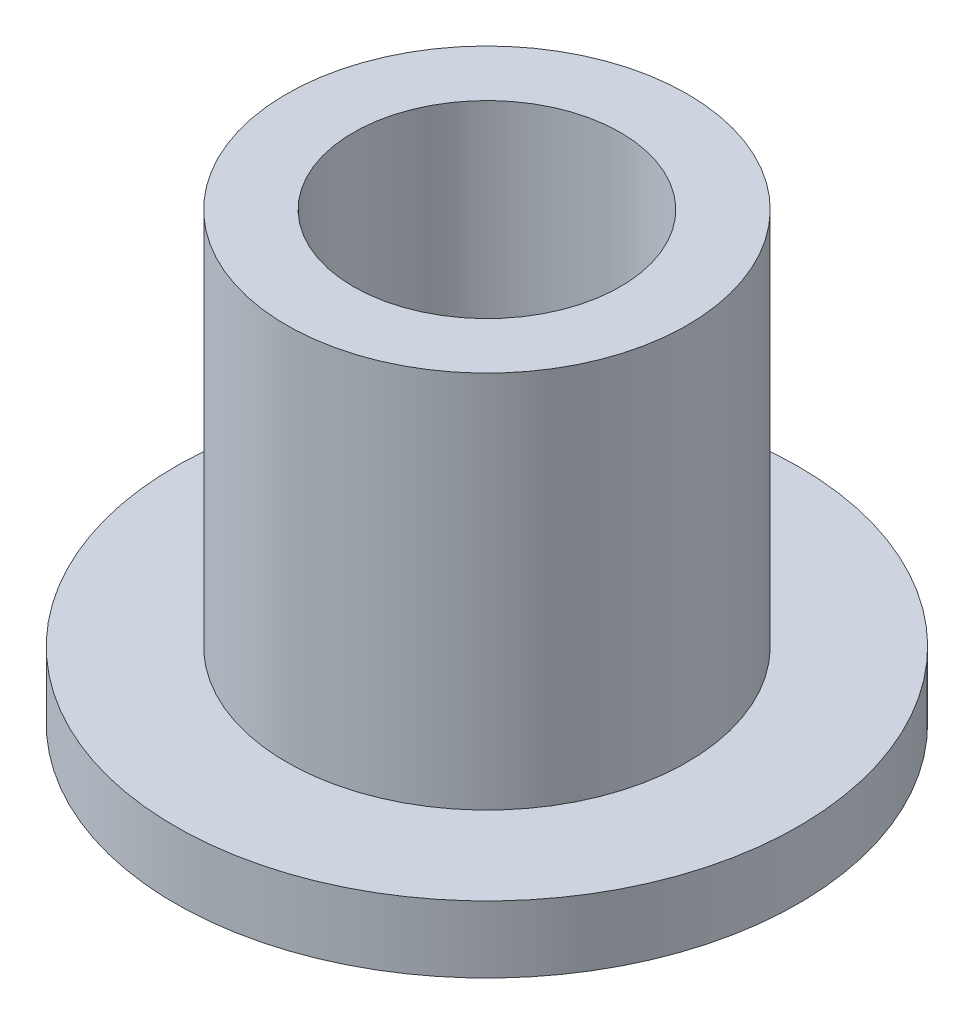
SolidWorks part; units mm, degrees
ref_plane "正面(Front)" through (0, 0, 0) normal (0, 0, 1) x (1, 0, 0)
ref_plane "平面(Top)" through (0, 0, 0) normal (0, 1, 0) x (1, 0, 0)
ref_plane "右側面(Right)" through (0, 0, 0) normal (1, 0, 0) x (0, 0, -1)
sketch "ｽｹｯﾁ1" plane through (0, 0, 0) normal (0, 0, 1) x (1, 0, 0)
  line L0 (0, 0) -> (0, 2.8823) construction
  line L1 (1.5, 0) -> (3.5, 0)
  line L2 (3.5, 0) -> (3.5, 0.75)
  line L3 (3.5, 0.75) -> (2.25, 0.75)
  line L4 (2.25, 0.75) -> (2.25, 5)
  line L5 (2.25, 5) -> (1.5, 5)
  line L6 (1.5, 5) -> (1.5, 0)
  point P3 (1.5, 0.0144)
  point P10 (0, 0)
  point P11 (2.9746, 0.1496)
  point P12 (0, 0)
  dimension "D1" = 3
  dimension "D2" = 4.5
  dimension "D3" = 0.75
  dimension "D4" = 5
  dimension "D5" = 7
revolve "回転1" add sketch "ｽｹｯﾁ1" angle 360 about L0
